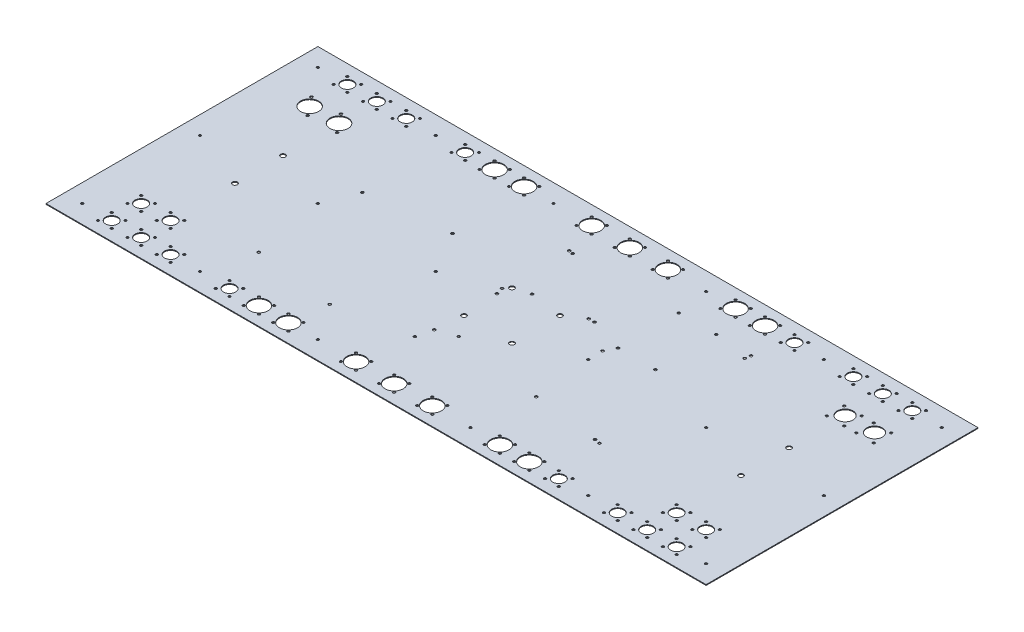
SolidWorks part; units mm, degrees
ref_plane "Front Plane" through (0, 0, 0) normal (0, 0, 1) x (1, 0, 0)
ref_plane "Top Plane" through (0, 0, 0) normal (0, 1, 0) x (1, 0, 0)
ref_plane "Right Plane" through (0, 0, 0) normal (1, 0, 0) x (0, 0, -1)
sketch "main_plate" plane through (0, 0, 0) normal (0, 1, 0) x (1, 0, 0)
  line L1 (-437, 180) -> (437, 180)
  line L2 (-437, 180) -> (-437, -180)
  line L3 (-437, -180) -> (437, -180)
  line L4 (437, 180) -> (437, -180)
  line L5 (-437, 180) -> (437, -180) construction
  line L6 (-437, -180) -> (437, 180) construction
  point P0 (0, 0)
  dimension "D1" = 360
  dimension "D2" = 874
extrude "Boss-Extrude1" add sketch "main_plate" along normal blind 1.016
sketch "main_holes" plane through (0, 1.016, 0) normal (0, 1, 0) x (1, 0, 0)
  line L0 (-437, 180) -> (-437, -180) construction
  line L1 (437, 180) -> (-437, 180) construction
  line L2 (-437, 0) -> (437, 0) construction
  line L3 (437, -180) -> (437, 180) construction
  line L4 (-437, -180) -> (437, -180) construction
  line L5 (0, 180) -> (0, -180) construction
  circle A0 centre (-413, 156) radius 1.6
  circle A3 centre (-335, 31.8059) radius 3.175
  circle A4 centre (-335, -31.8059) radius 3.175
  circle A6 centre (-257, 156) radius 1.6
  circle A7 centre (-101, 156) radius 1.6
  circle A8 centre (-257, 0) radius 1.6
  circle A9 centre (-101, 0) radius 1.6
  circle A10 centre (-257, -156) radius 1.6
  circle A11 centre (-101, -156) radius 1.6
  circle A12 centre (-413, 0) radius 1.6
  circle A13 centre (-413, -156) radius 1.6
  circle A14 centre (-31.75, 31.75) radius 3.175
  circle A15 centre (-31.75, -31.75) radius 3.175
  circle A16 centre (31.75, -31.75) radius 3.175
  circle A17 centre (31.75, 31.75) radius 3.175
  circle A18 centre (413, -156) radius 1.6
  circle A19 centre (413, 0) radius 1.6
  circle A20 centre (101, -156) radius 1.6
  circle A21 centre (257, -156) radius 1.6
  circle A22 centre (101, 0) radius 1.6
  circle A23 centre (257, 0) radius 1.6
  circle A24 centre (101, 156) radius 1.6
  circle A25 centre (257, 156) radius 1.6
  circle A26 centre (335, -31.8059) radius 3.175
  circle A27 centre (335, 31.8059) radius 3.175
  circle A28 centre (413, 156) radius 1.6
  dimension "D3" = 3.2
  dimension "D8" = 6.35
  dimension "D1" = 24
  dimension "D2" = 24
  dimension "D4" = 3
  dimension "D5" = 3
  dimension "D6" = 78
  dimension "D7" = 31.75
  dimension "D9" = 31.75
extrude "Cut-Extrude1" cut sketch "main_holes" against normal through all
sketch "fan" plane through (0, 1.016, 1.016) normal (0, 1, 0) x (1, 0, 0)
  line L0 (-101, 157.016) -> (101, 157.016) construction
  line L1 (-101, -154.984) -> (101, -154.984) construction
  line L2 (101, -154.984) -> (257, -154.984) construction
  line L3 (-257, -154.984) -> (-101, -154.984) construction
  circle A0 centre (-101, -154.984) radius 1.6 construction
  circle A1 centre (101, -154.984) radius 1.6 construction
  circle B0 centre (130, -144.984) radius 1.6
  circle B1 centre (150, -144.984) radius 1.6
  circle B2 centre (150, -164.984) radius 1.6
  circle B3 centre (130, -164.984) radius 1.6
  circle B4 centre (140, -154.984) radius 12
  circle B5 centre (169, -144.984) radius 1.6
  circle B6 centre (189, -144.984) radius 1.6
  circle B7 centre (189, -164.984) radius 1.6
  circle B8 centre (169, -164.984) radius 1.6
  circle B9 centre (179, -154.984) radius 12
  circle B10 centre (-10, -144.984) radius 1.6
  circle B11 centre (10, -144.984) radius 1.6
  circle B12 centre (10, -164.984) radius 1.6
  circle B13 centre (-10, -164.984) radius 1.6
  circle B14 centre (0, -154.984) radius 12
  circle B15 centre (-60.5, -144.984) radius 1.6
  circle B16 centre (-40.5, -144.984) radius 1.6
  circle B17 centre (-40.5, -164.984) radius 1.6
  circle B18 centre (-60.5, -164.984) radius 1.6
  circle B19 centre (-50.5, -154.984) radius 12
  circle B20 centre (40.5, -144.984) radius 1.6
  circle B21 centre (60.5, -144.984) radius 1.6
  circle B22 centre (60.5, -164.984) radius 1.6
  circle B23 centre (40.5, -164.984) radius 1.6
  circle B24 centre (50.5, -154.984) radius 12
  circle B25 centre (-10, 167.016) radius 1.6
  circle B26 centre (10, 167.016) radius 1.6
  circle B27 centre (10, 147.016) radius 1.6
  circle B28 centre (-10, 147.016) radius 1.6
  circle B29 centre (0, 157.016) radius 12
  circle B30 centre (-60.5, 167.016) radius 1.6
  circle B31 centre (-40.5, 167.016) radius 1.6
  circle B32 centre (-40.5, 147.016) radius 1.6
  circle B33 centre (-60.5, 147.016) radius 1.6
  circle B34 centre (-50.5, 157.016) radius 12
  circle B35 centre (40.5, 167.016) radius 1.6
  circle B36 centre (60.5, 167.016) radius 1.6
  circle B37 centre (60.5, 147.016) radius 1.6
  circle B38 centre (40.5, 147.016) radius 1.6
  circle B39 centre (50.5, 157.016) radius 12
  circle B40 centre (-189, -144.984) radius 1.6
  circle B41 centre (-169, -144.984) radius 1.6
  circle B42 centre (-169, -164.984) radius 1.6
  circle B43 centre (-189, -164.984) radius 1.6
  circle B44 centre (-179, -154.984) radius 12
  circle B45 centre (-150, -144.984) radius 1.6
  circle B46 centre (-130, -144.984) radius 1.6
  circle B47 centre (-130, -164.984) radius 1.6
  circle B48 centre (-150, -164.984) radius 1.6
  circle B49 centre (-140, -154.984) radius 12
  circle B50 centre (-189, 167.016) radius 1.6
  circle B51 centre (-169, 167.016) radius 1.6
  circle B52 centre (-169, 147.016) radius 1.6
  circle B53 centre (-189, 147.016) radius 1.6
  circle B54 centre (-179, 157.016) radius 12
  circle B55 centre (-150, 167.016) radius 1.6
  circle B56 centre (-130, 167.016) radius 1.6
  circle B57 centre (-130, 147.016) radius 1.6
  circle B58 centre (-150, 147.016) radius 1.6
  circle B59 centre (-140, 157.016) radius 12
  circle B60 centre (130, 167.016) radius 1.6
  circle B61 centre (150, 167.016) radius 1.6
  circle B62 centre (150, 147.016) radius 1.6
  circle B63 centre (130, 147.016) radius 1.6
  circle B64 centre (140, 157.016) radius 12
  circle B65 centre (169, 167.016) radius 1.6
  circle B66 centre (189, 167.016) radius 1.6
  circle B67 centre (189, 147.016) radius 1.6
  circle B68 centre (169, 147.016) radius 1.6
  circle B69 centre (179, 157.016) radius 12
  dimension "D1" = 39
  dimension "D2" = 202
  dimension "D4" = 39
  dimension "D6" = 39
  dimension "D7" = 39
  dimension "D3" = 50.5
sketch_block_instance "Block2-11"
sketch_block "Block2" parameters "D1"=3.2, "D2"=24, "D3"=10, "D4"=10, "D5"=10, "D6"=10
sketch_block_instance "Block2-12"
sketch_block_instance "Block13-1"
sketch_block "Block13"
sketch_block_instance "Block2-16"
sketch_block_instance "Block2-15"
sketch_block_instance "Block2-17"
sketch_block_instance "Block2-19"
sketch_block_instance "Block13-2"
sketch_block_instance "Block14-1"
sketch_block "Block14"
sketch_block_instance "Block2-18"
sketch_block_instance "Block2-10"
sketch_block_instance "Block14-2"
sketch_block_instance "Block14-3"
extrude "Cut-Extrude2" cut sketch "fan" against normal through all
sketch "ntype" plane through (0, 1.016, 0) normal (0, 1, 0) x (1, 0, 0)
  line L1 (-413, -156) -> (413, -156) construction
  line L2 (413, -156) -> (413, 156) construction
  line L3 (413, 156) -> (-413, 156) construction
  line L4 (-413, 156) -> (-413, -156) construction
  circle A1 centre (-257, 156) radius 1.6 construction
  circle A2 centre (413, 156) radius 1.6 construction
  circle A3 centre (-257, -156) radius 1.6 construction
  circle A4 centre (257, -156) radius 1.6 construction
  circle A5 centre (257, 156) radius 1.6 construction
  circle B0 centre (-218, 156) radius 8
  circle B1 centre (-227.1, 165.1) radius 1.6
  circle B2 centre (-208.9, 165.1) radius 1.6
  circle B3 centre (-208.9, 146.9) radius 1.6
  circle B4 centre (-227.1, 146.9) radius 1.6
  circle B5 centre (218, 156) radius 8
  circle B6 centre (208.9, 165.1) radius 1.6
  circle B7 centre (227.1, 165.1) radius 1.6
  circle B8 centre (227.1, 146.9) radius 1.6
  circle B9 centre (208.9, 146.9) radius 1.6
  circle B10 centre (-218, -156) radius 8
  circle B11 centre (-227.1, -146.9) radius 1.6
  circle B12 centre (-208.9, -146.9) radius 1.6
  circle B13 centre (-208.9, -165.1) radius 1.6
  circle B14 centre (-227.1, -165.1) radius 1.6
  circle B15 centre (218, -156) radius 8
  circle B16 centre (208.9, -146.9) radius 1.6
  circle B17 centre (227.1, -146.9) radius 1.6
  circle B18 centre (227.1, -165.1) radius 1.6
  circle B19 centre (208.9, -165.1) radius 1.6
  circle B20 centre (-374, 156) radius 8
  circle B21 centre (-383.1, 165.1) radius 1.6
  circle B22 centre (-364.9, 165.1) radius 1.6
  circle B23 centre (-364.9, 146.9) radius 1.6
  circle B24 centre (-383.1, 146.9) radius 1.6
  circle B25 centre (-296, 156) radius 8
  circle B26 centre (-305.1, 165.1) radius 1.6
  circle B27 centre (-286.9, 165.1) radius 1.6
  circle B28 centre (-286.9, 146.9) radius 1.6
  circle B29 centre (-305.1, 146.9) radius 1.6
  circle B30 centre (-335, 156) radius 8
  circle B31 centre (-344.1, 165.1) radius 1.6
  circle B32 centre (-325.9, 165.1) radius 1.6
  circle B33 centre (-325.9, 146.9) radius 1.6
  circle B34 centre (-344.1, 146.9) radius 1.6
  circle B35 centre (296, -156) radius 8
  circle B36 centre (286.9, -146.9) radius 1.6
  circle B37 centre (305.1, -146.9) radius 1.6
  circle B38 centre (305.1, -165.1) radius 1.6
  circle B39 centre (286.9, -165.1) radius 1.6
  circle B40 centre (374, -156) radius 8
  circle B41 centre (364.9, -146.9) radius 1.6
  circle B42 centre (383.1, -146.9) radius 1.6
  circle B43 centre (383.1, -165.1) radius 1.6
  circle B44 centre (364.9, -165.1) radius 1.6
  circle B45 centre (335, -156) radius 8
  circle B46 centre (325.9, -146.9) radius 1.6
  circle B47 centre (344.1, -146.9) radius 1.6
  circle B48 centre (344.1, -165.1) radius 1.6
  circle B49 centre (325.9, -165.1) radius 1.6
  circle B50 centre (296, 156) radius 8
  circle B51 centre (286.9, 165.1) radius 1.6
  circle B52 centre (305.1, 165.1) radius 1.6
  circle B53 centre (305.1, 146.9) radius 1.6
  circle B54 centre (286.9, 146.9) radius 1.6
  circle B55 centre (374, 156) radius 8
  circle B56 centre (364.9, 165.1) radius 1.6
  circle B57 centre (383.1, 165.1) radius 1.6
  circle B58 centre (383.1, 146.9) radius 1.6
  circle B59 centre (364.9, 146.9) radius 1.6
  circle B60 centre (335, 156) radius 8
  circle B61 centre (325.9, 165.1) radius 1.6
  circle B62 centre (344.1, 165.1) radius 1.6
  circle B63 centre (344.1, 146.9) radius 1.6
  circle B64 centre (325.9, 146.9) radius 1.6
  circle B65 centre (-374, -156) radius 8
  circle B66 centre (-383.1, -146.9) radius 1.6
  circle B67 centre (-364.9, -146.9) radius 1.6
  circle B68 centre (-364.9, -165.1) radius 1.6
  circle B69 centre (-383.1, -165.1) radius 1.6
  circle B70 centre (-296, -156) radius 8
  circle B71 centre (-305.1, -146.9) radius 1.6
  circle B72 centre (-286.9, -146.9) radius 1.6
  circle B73 centre (-286.9, -165.1) radius 1.6
  circle B74 centre (-305.1, -165.1) radius 1.6
  circle B75 centre (-335, -156) radius 8
  circle B76 centre (-344.1, -146.9) radius 1.6
  circle B77 centre (-325.9, -146.9) radius 1.6
  circle B78 centre (-325.9, -165.1) radius 1.6
  circle B79 centre (-344.1, -165.1) radius 1.6
  circle B80 centre (-335, -117) radius 8
  circle B81 centre (-344.1, -107.9) radius 1.6
  circle B82 centre (-325.9, -107.9) radius 1.6
  circle B83 centre (-325.9, -126.1) radius 1.6
  circle B84 centre (-344.1, -126.1) radius 1.6
  circle B85 centre (-374, -117) radius 8
  circle B86 centre (-383.1, -107.9) radius 1.6
  circle B87 centre (-364.9, -107.9) radius 1.6
  circle B88 centre (-364.9, -126.1) radius 1.6
  circle B89 centre (-383.1, -126.1) radius 1.6
  circle B90 centre (374, -117) radius 8
  circle B91 centre (364.9, -107.9) radius 1.6
  circle B92 centre (383.1, -107.9) radius 1.6
  circle B93 centre (383.1, -126.1) radius 1.6
  circle B94 centre (364.9, -126.1) radius 1.6
  circle B95 centre (335, -117) radius 8
  circle B96 centre (325.9, -107.9) radius 1.6
  circle B97 centre (344.1, -107.9) radius 1.6
  circle B98 centre (344.1, -126.1) radius 1.6
  circle B99 centre (325.9, -126.1) radius 1.6
  dimension "D1" = 156
  dimension "D2" = 39
  dimension "D4" = 39
  dimension "D3" = 39
  dimension "D5" = 39
  dimension "D6" = 39
  dimension "D7" = 39
  dimension "D8" = 39
  dimension "D9" = 39
  dimension "D10" = 39
  dimension "D11" = 39
sketch_block_instance "Block3-10"
sketch_block "Block3" parameters "D1"=3.2, "D2"=16, "D3"=9.1, "D4"=9.1, "D5"=9.1, "D6"=9.1
sketch_block_instance "Block3-16"
sketch_block_instance "Block3-17"
sketch_block_instance "Block3-18"
sketch_block_instance "Block3-19"
sketch_block_instance "Block11-1"
sketch_block "Block11"
sketch_block_instance "Block3-24"
sketch_block_instance "Block3-23"
sketch_block_instance "Block3-21"
sketch_block_instance "Block11-2"
sketch_block_instance "Block11-3"
sketch_block_instance "Block11-4"
sketch_block_instance "Block12-1"
sketch_block "Block12"
sketch_block_instance "Block3-27"
sketch_block_instance "Block3-28"
sketch_block_instance "Block12-2"
extrude "Cut-Extrude3" cut sketch "ntype" against normal through all
sketch "ethernet" plane through (0, 1.016, 0) normal (0, 1, 0) x (1, 0, 0)
  circle A1 centre (-413, 156) radius 1.6 construction
  circle B0 centre (-374, 106) radius 12
  circle B1 centre (-383.5, 118) radius 1.755
  circle B2 centre (-364.5, 94) radius 1.755
  circle B3 centre (-335, 106) radius 12
  circle B4 centre (-344.5, 118) radius 1.755
  circle B5 centre (-325.5, 94) radius 1.755
  dimension "D1" = 39
  dimension "D2" = 2
  dimension "D3" = 50
sketch_block_instance "Block9-1"
sketch_block "Block9" parameters "D1"=24, "D2"=3.51, "D3"=19, "D4"=24, "D5"=9.5, "D6"=12
sketch_block_instance "Block9-3"
extrude "Cut-Extrude6" cut sketch "ethernet" against normal blind 10
sketch "power" plane through (0, 1.016, 0) normal (0, 1, 0) x (1, 0, 0)
  circle A0 centre (413, 156) radius 1.6 construction
  circle B0 centre (374, 106) radius 10.4521
  circle B1 centre (362.4938, 116.4521) radius 1.5875
  circle B2 centre (385.5062, 116.4521) radius 1.5875
  circle B3 centre (385.5062, 93.4397) radius 1.5875
  circle B4 centre (362.4938, 93.4397) radius 1.5875
  circle B5 centre (335, 106) radius 10.4521
  circle B6 centre (323.4938, 116.4521) radius 1.5875
  circle B7 centre (346.5062, 116.4521) radius 1.5875
  circle B8 centre (346.5062, 93.4397) radius 1.5875
  circle B9 centre (323.4938, 93.4397) radius 1.5875
  dimension "D1" = 39
  dimension "D2" = 50
  dimension "D3" = 2
sketch_block_instance "Block10-1"
sketch_block "Block10" parameters "D1"=20.9042, "D2"=3.175, "D3"=10.4521, "D4"=23.0124, "D5"=11.5062
sketch_block_instance "Block10-2"
extrude "Cut-Extrude7" cut sketch "power" against normal blind 10
sketch "ads9+eval" plane through (0, 1.016, -2.032) normal (0, 1, 0) x (-1, 0, 0)
  line L4 (-210.8431, 97.5203) -> (48.8669, 97.5203) construction
  line L5 (-210.8431, 97.5203) -> (-210.8431, -118.3797) construction
  line L6 (-210.8431, -118.3797) -> (48.8669, -118.3797) construction
  line L9 (48.8669, 97.5203) -> (48.8669, -118.3797) construction
  line L10 (-210.8431, 97.5203) -> (48.8669, -118.3797) construction
  line L11 (-210.8431, -118.3797) -> (48.8669, 97.5203) construction
  line L17 (20.0506, 28.6273) -> (256.7786, 28.5003) construction
  line L18 (38.8466, 125.0203) -> (256.7786, 125.0203) construction
  line L19 (38.8466, 125.0203) -> (38.8466, 63.8063) construction
  line L20 (38.8466, -68.0197) -> (256.7786, -68.0197) construction
  line L21 (256.7786, 125.0203) -> (256.7786, -68.0197) construction
  line L22 (38.8466, 125.0203) -> (256.7786, -68.0197) construction
  line L23 (38.8466, -68.0197) -> (256.7786, 125.0203) construction
  line L24 (20.0506, 63.8063) -> (38.8466, 63.8063) construction
  line L25 (20.0506, 63.8063) -> (20.0506, -6.5517) construction
  line L26 (20.0506, -6.5517) -> (38.8466, -6.5517) construction
  line L27 (38.8466, -68.0197) -> (38.8466, -6.5517) construction
  circle A20 centre (-204.3631, 90.5003) radius 1.75
  circle A21 centre (-197.1231, 89.1803) radius 1.75
  circle A22 centre (-203.1031, -102.9797) radius 1.75
  circle A23 centre (-204.3731, -110.1597) radius 1.75
  circle A24 centre (-62.1331, -45.0697) radius 1.75
  circle A25 centre (-54.5131, -45.0697) radius 1.75
  circle A26 centre (11.3469, -35.8197) radius 1.75
  circle A27 centre (-100.4131, -17.4397) radius 1.75
  circle A28 centre (37.7369, -22.5297) radius 1.75
  circle A29 centre (35.0269, -13.0597) radius 1.75
  circle A30 centre (30.8269, -109.1997) radius 1.75
  circle A31 centre (36.4694, -110.1597) radius 1.75
  circle A32 centre (11.3569, 61.2103) radius 1.75
  circle A33 centre (35.1869, 69.7403) radius 1.75
  circle A34 centre (40.1069, 90.5003) radius 1.75
  circle A35 centre (-109.1131, 79.1103) radius 1.75
  circle A36 centre (133.5566, 109.8465) radius 1.75
  circle A37 centre (240.2366, 97.0892) radius 1.75
  circle A38 centre (240.163, -40.0708) radius 1.75
  circle A39 centre (133.4694, -52.7135) radius 1.75
  circle A40 centre (-157.0021, -111.3662) radius 1.75
  circle A41 centre (-107.4721, -111.3662) radius 1.75
  circle A42 centre (-157.0021, -30.8482) radius 1.75
  circle A43 centre (-107.4721, -30.8482) radius 1.75
  point P0 (-80.9881, -10.4297)
  point P37 (147.8126, 28.5003)
  dimension "D6" = 3.5
  dimension "D44" = 3.5
  dimension "D1" = 27.5
  dimension "D2" = 97
  dimension "D3" = 100.3781
  dimension "D4" = 215.9
  dimension "D5" = 259.71
  dimension "D7" = 6.48
  dimension "D8" = 7.24
  dimension "D9" = 111
  dimension "D10" = 103.38
  dimension "D11" = 18.04
  dimension "D12" = 12.3976
  dimension "D13" = 37.52
  dimension "D14" = 11.13
  dimension "D15" = 13.84
  dimension "D16" = 110.43
  dimension "D17" = 101.73
  dimension "D18" = 7.74
  dimension "D19" = 6.47
  dimension "D20" = 37.51
  dimension "D21" = 13.68
  dimension "D22" = 8.76
  dimension "D23" = 15.4
  dimension "D24" = 8.22
  dimension "D25" = 100.94
  dimension "D26" = 7.02
  dimension "D27" = 8.34
  dimension "D28" = 18.41
  dimension "D29" = 36.31
  dimension "D30" = 27.78
  dimension "D31" = 7.02
  dimension "D32" = 8.22
  dimension "D33" = 9.18
  dimension "D34" = 73.31
  dimension "D35" = 73.31
  dimension "D36" = 82.56
  dimension "D37" = 105.32
  dimension "D38" = 95.85
  dimension "D39" = 217.932
  dimension "D40" = 70.358
  dimension "D41" = 61.468
  dimension "D42" = 193.04
  dimension "D43" = 18.796
  dimension "D45" = 81.28
  dimension "D46" = 68.58
  dimension "D47" = 94.71
  dimension "D48" = 106.68
  dimension "D49" = 47.371
  dimension "D50" = 49.53
  dimension "D51" = 80.518
  dimension "D52" = 1.2065
extrude "Cut-Extrude8" cut sketch "ads9+eval" against normal blind 10
